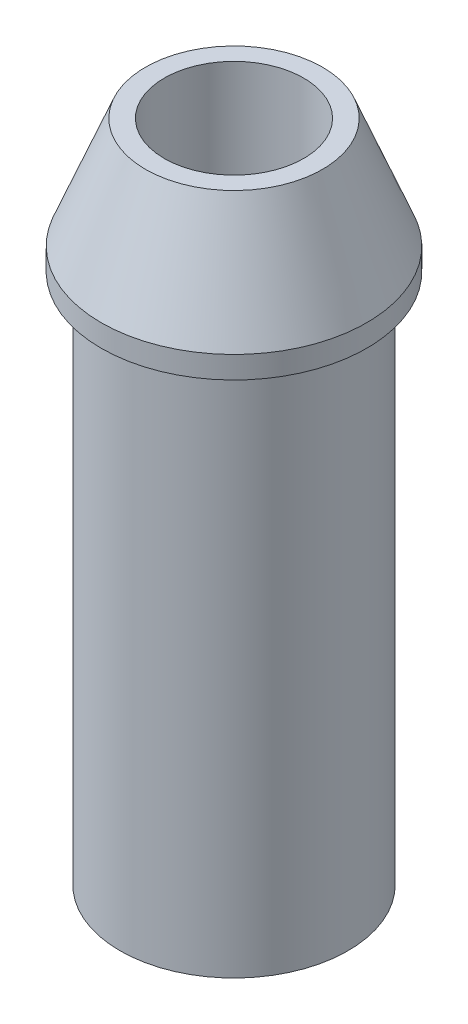
SolidWorks part; units mm, degrees
ref_plane "Front Plane" through (0, 0, 0) normal (0, 0, 1) x (1, 0, 0)
ref_plane "Top Plane" through (0, 0, 0) normal (0, 1, 0) x (1, 0, 0)
ref_plane "Right Plane" through (0, 0, 0) normal (1, 0, 0) x (0, 0, -1)
sketch "Sketch1" plane through (0, 0, 0) normal (0, 1, 0) x (1, 0, 0)
  circle A0 centre (0, 0) radius 1.575
  circle A1 centre (0, 0) radius 2.575
  dimension "D1" = 5.15
  dimension "D2" = 3.15
extrude "Boss-Extrude1" add sketch "Sketch1" along normal blind 15
sketch "Sketch2" plane through (0, 15, 0) normal (0, 1, 0) x (1, 0, 0)
  circle A0 centre (0, 0) radius 3
  circle A1 centre (0, 0) radius 1.575 construction
  circle A2 centre (0, 0) radius 1.575
  dimension "D1" = 6
extrude "Boss-Extrude2" add sketch "Sketch2" against normal blind 3
chamfer "Chamfer1" distance 2.5 distance2 1 1 edges at (0, 15, 3)
